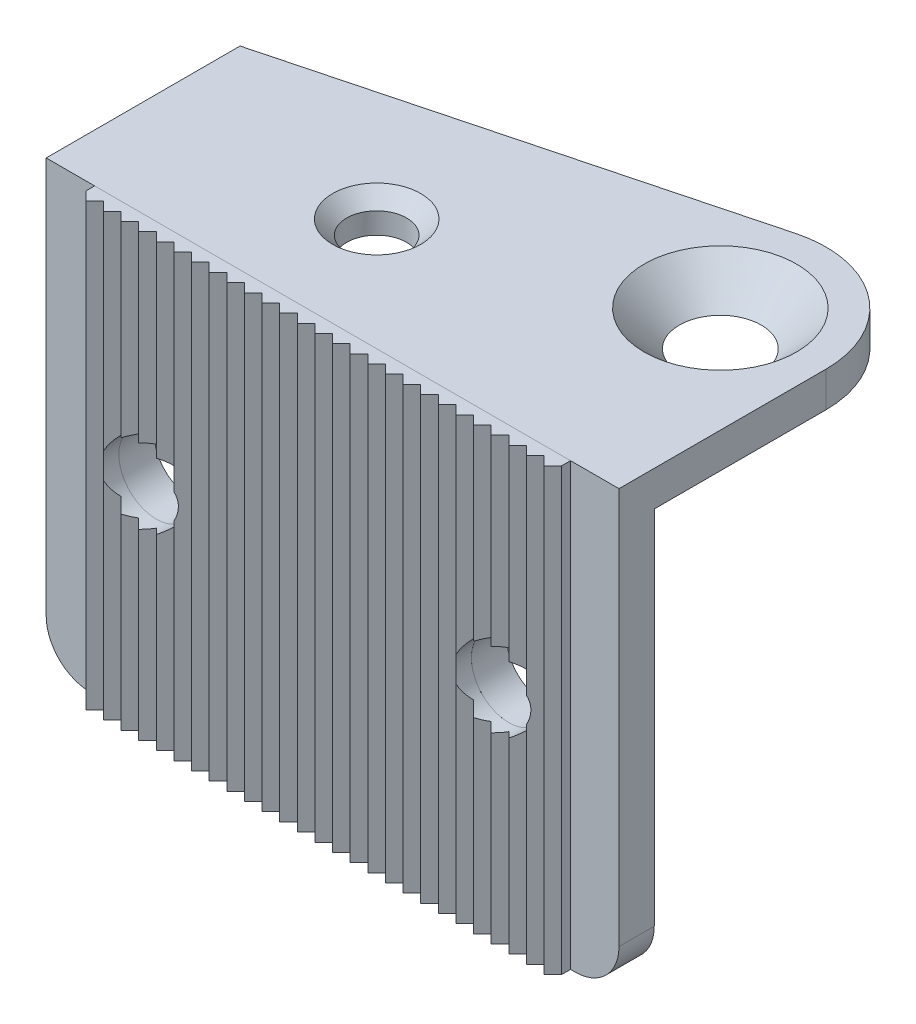
SolidWorks part; units mm, degrees
material "Alu 5754 (AG3)"
ref_plane "Face" through (0, 0, 0) normal (0, 0, 1) x (1, 0, 0)
ref_plane "Dessus" through (0, 0, 0) normal (0, 1, 0) x (1, 0, 0)
ref_plane "Droite" through (0, 0, 0) normal (1, 0, 0) x (0, 0, -1)
sketch "Esquisse1" plane through (0, 0, 0) normal (0, 0, 1) x (1, 0, 0)
  line L1 (-32.5, 25) -> (32.5, 25)
  line L2 (-32.5, 25) -> (-32.5, -20)
  line L3 (-27.5, -25) -> (27.5, -25)
  line L4 (32.5, 25) -> (32.5, -20)
  line L5 (-32.5, 25) -> (32.5, -25) construction
  line L6 (-32.5, -25) -> (32.5, 25) construction
  arc A0 (27.5, -25) -> (32.5, -20) centre (27.5, -20) ccw
  arc A1 (-32.5, -20) -> (-27.5, -25) centre (-27.5, -20) ccw
  point P0 (0, 0)
  dimension "D3" = 5
  dimension "D1" = 65
  dimension "D2" = 50
extrude "Boss.-Extru.1" add sketch "Esquisse1" along normal blind 4
sketch "Esquisse2" plane through (0, 25, 0) normal (0, 1, 0) x (1, 0, 0)
  line L0 (-32.5, 0) -> (-32.5, 18)
  line L1 (-32.5, 18) -> (17.4545, 31.1071)
  line L2 (32.5, 19.5) -> (32.5, 0)
  line L3 (32.5, 0) -> (-32.5, 0)
  arc A0 (17.4545, 31.1071) -> (32.5, 19.5) centre (20.5, 19.5) cw
  point P8 (20.5, 31.5)
  dimension "D2" = 12
  dimension "D1" = 18
  dimension "D3" = 31.5
extrude "Boss.-Extru.2" add sketch "Esquisse2" against normal blind 4
sketch "Esquisse3" plane through (0, 0, 4) normal (0, 0, 1) x (1, 0, 0)
  line L0 (0, 0) -> (0, -25) construction
  line L1 (-27.5, -25) -> (27.5, -25) construction
  circle A0 centre (20, 0) radius 4.25
  circle A1 centre (-20, 0) radius 4.25
  dimension "D2" = 8.5
  dimension "D3" = 25
  dimension "D1" = 20
extrude "Enlèv. mat.-Extru.1" cut sketch "Esquisse3" against normal up to surface (4 mm away) up to face at (-5.4167, -8.3452, 0)
hole_wizard "Fraisage pour vis à tête fraisée M81" positions "Esquisse5" profile "Esquisse4" countersink size "M8" standard "ISO" end condition through all
sketch "Esquisse5" plane through (0, 25, 0) normal (0, 1, 0) x (1, 0, 0)
  point P0 (20.5, 19.5)
sketch "Esquisse4" plane through (20.5, 25, -19.5) normal (1, 0, 0) x (0, 0, 1)
  line L0 (0, 0) -> (0, 50)
  line L1 (0, 50) -> (4.5, 50)
  line L2 (4.5, 50) -> (4.5, 4.15)
  line L3 (4.5, 4.15) -> (8.65, 0)
  line L5 (8.65, 0) -> (0, 0)
  line L6 (-4.5, 4.15) -> (-8.65, 0) construction
  line L11 (0, -6.35) -> (0, 107.95) construction
  dimension "Diamètre du perçage jusqu'au prochain" = 9
  dimension "Profondeur du perçage jusqu'au prochain" = 50
  dimension "Diamètre du fraisage entrant" = 17.3
  dimension "Angle du fraisage entrant" = 90
hole_wizard "Trou taraudé M81" positions "Esquisse7" profile "Esquisse6" tap size "M8" standard "ISO" end condition through all
sketch "Esquisse7" plane through (0, 25, 0) normal (0, 1, 0) x (1, 0, 0)
  point P0 (-7.75, 8.7537)
sketch "Esquisse6" plane through (-7.75, 25, -8.7537) normal (1, 0, 0) x (0, 0, 1)
  line L0 (0, 0) -> (0, 50)
  line L1 (0, 50) -> (3.4, 50)
  line L2 (3.4, 50) -> (3.4, 1.6)
  line L3 (3.4, 1.6) -> (5, 0)
  line L5 (5, 0) -> (0, 0)
  line L6 (-3.4, 1.6) -> (-5, 0) construction
  line L11 (0, -6.35) -> (0, 107.95) construction
  dimension "Diamètre du trou pour taraudage jusqu'au prochain" = 6.8
  dimension "Profondeur du trou pour taraudage jusqu'au prochain" = 50
  dimension "Diamètre du fraisage entrant" = 10
  dimension "Angle du fraisage entrant" = 90
cosmetic thread "Filetage de perçage1" parameters "D2"=8
sketch "Esquisse8" plane through (0, -25, 0) normal (0, -1, 0) x (1, 0, 0)
  line L0 (27, 4) -> (27, 5)
  line L1 (27, 5) -> (26, 6)
  line L2 (26, 6) -> (25, 5)
  line L3 (32.5, 4) -> (27.5, 4) construction
  line L5 (-27.5, 4) -> (27.5, 4) construction
  line L6 (25, 5) -> (24, 6)
  line L7 (24, 6) -> (23, 5)
  line L8 (23, 5) -> (22, 6)
  line L9 (22, 6) -> (21, 5)
  line L10 (21, 5) -> (20, 6)
  line L11 (20, 6) -> (19, 5)
  line L12 (19, 5) -> (18, 6)
  line L13 (18, 6) -> (17, 5)
  line L14 (17, 5) -> (16, 6)
  line L15 (16, 6) -> (15, 5)
  line L16 (15, 5) -> (14, 6)
  line L17 (14, 6) -> (13, 5)
  line L18 (13, 5) -> (12, 6)
  line L19 (12, 6) -> (11, 5)
  line L20 (11, 5) -> (10, 6)
  line L21 (10, 6) -> (9, 5)
  line L22 (9, 5) -> (8, 6)
  line L23 (8, 6) -> (7, 5)
  line L24 (7, 5) -> (6, 6)
  line L25 (6, 6) -> (5, 5)
  line L26 (5, 5) -> (4, 6)
  line L27 (4, 6) -> (3, 5)
  line L28 (3, 5) -> (2, 6)
  line L29 (2, 6) -> (1, 5)
  line L30 (1, 5) -> (0, 6)
  line L31 (0, 6) -> (-1, 5)
  line L32 (-1, 5) -> (-2, 6)
  line L33 (-2, 6) -> (-3, 5)
  line L34 (-3, 5) -> (-4, 6)
  line L35 (-4, 6) -> (-5, 5)
  line L36 (-5, 5) -> (-6, 6)
  line L37 (-6, 6) -> (-7, 5)
  line L38 (-7, 5) -> (-8, 6)
  line L39 (-8, 6) -> (-9, 5)
  line L40 (-9, 5) -> (-10, 6)
  line L41 (-10, 6) -> (-11, 5)
  line L42 (-11, 5) -> (-12, 6)
  line L43 (-12, 6) -> (-13, 5)
  line L44 (-13, 5) -> (-14, 6)
  line L45 (-14, 6) -> (-15, 5)
  line L46 (-15, 5) -> (-16, 6)
  line L47 (-16, 6) -> (-17, 5)
  line L48 (-17, 5) -> (-18, 6)
  line L49 (-18, 6) -> (-19, 5)
  line L50 (-19, 5) -> (-20, 6)
  line L51 (-20, 6) -> (-21, 5)
  line L52 (-21, 5) -> (-22, 6)
  line L53 (-22, 6) -> (-23, 5)
  line L54 (-23, 5) -> (-24, 6)
  line L55 (-24, 6) -> (-25, 5)
  line L56 (-25, 5) -> (-26, 6)
  line L57 (-26, 6) -> (-27, 5)
  line L59 (-27, 5) -> (-27, 4)
  line L60 (-27, 4) -> (27, 4)
  line L61 (27.5, 4) -> (27.5, 0) construction
  dimension "D1" = 1
  dimension "D2" = 2
  dimension "D3" = 45
  dimension "D5" = 0.5
  dimension "D4" = 27
extrude "Boss.-Extru.3" add sketch "Esquisse8" against normal up to surface (50 mm away) separate body up to face at (-7.75, 25, -3.7537)
sketch "Esquisse9" plane through (0, 0, 4) normal (0, 0, -1) x (-1, 0, 0)
  circle A0 centre (-20, 0) radius 4.25 construction
  circle A1 centre (20, 0) radius 4.25 construction
  circle A2 centre (-20, 0) radius 4.25
  circle A3 centre (20, 0) radius 4.25
extrude "Enlèv. mat.-Extru.2" cut sketch "Esquisse9" against normal through all
